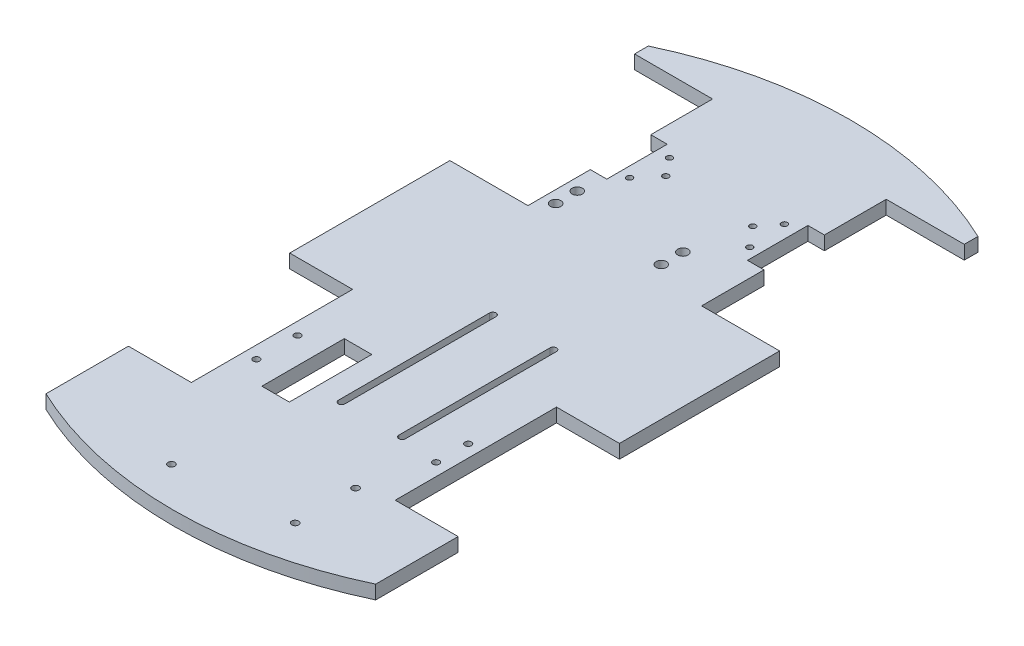
SolidWorks part; units mm, degrees
material "Oak"
ref_plane "Front Plane" through (0, 0, 0) normal (0, 0, 1) x (1, 0, 0)
ref_plane "Top Plane" through (0, 0, 0) normal (0, 1, 0) x (1, 0, 0)
ref_plane "Right Plane" through (0, 0, 0) normal (1, 0, 0) x (0, 0, -1)
sketch "Sketch1" plane through (0, 0, 0) normal (0, 1, 0) x (1, 0, 0)
  line L0 (50.292, 32.512) -> (76.2, 32.512) construction
  line L1 (0, 0) -> (0, -280.955) construction
  line L2 (0, 66.1738) -> (0, -229.362)
  line L3 (76.2, -229.362) -> (0, -229.362)
  line L7 (50.292, 32.512) -> (50.292, -32.512) construction
  line L8 (50.292, -32.512) -> (76.2, -32.512) construction
  line L9 (76.2, 32.512) -> (76.2, -32.512) construction
  line L10 (50.292, 32.512) -> (76.2, -32.512) construction
  line L11 (50.292, -32.512) -> (76.2, 32.512) construction
  line L18 (50.292, -119.888) -> (76.2, -119.888) construction
  line L19 (50.292, -119.888) -> (50.292, -184.912) construction
  line L20 (50.292, -184.912) -> (76.2, -184.912) construction
  line L21 (76.2, -119.888) -> (76.2, -184.912) construction
  line L22 (50.292, -119.888) -> (76.2, -184.912) construction
  line L23 (50.292, -184.912) -> (76.2, -119.888) construction
  line L25 (-76.2, 0) -> (76.2, 0) construction
  line L27 (-76.2, -152.4) -> (76.2, -152.4) construction
  line L28 (76.2, 0) -> (76.2, -152.4) construction
  line L33 (40.132, -42.672) -> (76.2, -42.672)
  line L34 (40.132, 42.672) -> (40.132, 14.097)
  line L35 (40.132, 42.672) -> (76.2, 42.672)
  line L36 (47.117, -191.262) -> (76.2, -191.262)
  line L37 (47.117, -116.713) -> (47.117, -191.262)
  line L38 (47.117, -116.713) -> (76.2, -116.713)
  line L43 (76.2, -42.672) -> (76.2, -116.713)
  line L45 (76.2, 42.672) -> (76.2, 49.022)
  line L47 (76.2, -191.262) -> (76.2, -229.362)
  line L55 (32.512, -13.843) -> (40.132, -13.843)
  line L56 (32.512, 14.097) -> (32.512, -13.843)
  line L57 (32.512, 14.097) -> (40.132, 14.097)
  line L58 (40.132, -13.843) -> (40.132, -42.672)
  arc A0 (0, 66.1738) -> (76.2, 49.022) centre (0, -111.6688) cw
  arc A1 (76.2, -229.362) -> (0, -252.984) centre (-13.2044, -75.675) cw
  point P9 (63.246, 0)
  point P19 (63.246, -152.4)
  dimension "D7" = 3.175
  dimension "D8" = 6.35
  dimension "D12" = 7.62
  dimension "D16" = 6.35
  dimension "D17" = 177.8426
  dimension "D18" = 177.8
  dimension "D1" = 152.4
  dimension "D2" = 152.4
  dimension "D3" = 126.492
  dimension "D4" = 25.908
  dimension "D6" = 3.175
  dimension "D9" = 10.16
  dimension "D10" = 10.16
  dimension "D5" = 65.024
  dimension "D11" = 10.16
  dimension "D13" = 27.94
  dimension "D14" = 28.575
  dimension "D15" = 38.1
  dimension "D19" = 23.622
extrude "Chassis" add sketch "Sketch1" along normal blind 6.35
mirror "Mirror1" about plane through (0, 6.35, 0) normal (1, 0, 0) of "Chassis"
sketch "Sketch4" plane through (0, 6.35, 0) normal (0, 1, 0) x (1, 0, 0)
  line L0 (76.2, -229.362) -> (-76.2, -229.362)
  arc A0 (76.2, -229.362) -> (-76.2, -229.362) centre (0, -68.7183) cw
  dimension "D1" = 177.8
extrude "Boss-Extrude1" add sketch "Sketch4" against normal blind 6.35 contours A0 L0
sketch "Sketch2" plane through (0, 0, 0) normal (0, 1, 0) x (1, 0, 0)
  line L0 (-47.117, -116.713) -> (-47.117, -191.262) construction
  line L1 (-47.117, -191.262) -> (-76.2, -191.262) construction
  line L2 (47.117, -116.713) -> (47.117, -191.262) construction
  line L3 (47.117, -191.262) -> (76.2, -191.262) construction
  line L4 (24.892, -94.488) -> (24.892, -164.338)
  line L5 (21.892, -94.488) -> (21.892, -164.338)
  line L6 (-3.048, -94.488) -> (-3.048, -164.338)
  line L7 (-6.048, -94.488) -> (-6.048, -164.338)
  line L8 (47.117, -116.713) -> (76.2, -116.713) construction
  line L10 (-16.637, -176.45) -> (-29.337, -176.45)
  line L11 (-16.637, -176.45) -> (-16.637, -138.35)
  line L12 (-16.637, -138.35) -> (-29.337, -138.35)
  line L13 (-29.337, -176.45) -> (-29.337, -138.35)
  circle A0 centre (-26.5557, 9.17) radius 1.3716 construction
  circle A2 centre (33.0969, -195.58) radius 1.5875
  circle A3 centre (-18.9731, -228.6) radius 1.5875
  circle A4 centre (-18.9731, -228.6) radius 1.5875
  circle A5 centre (33.0969, -223.52) radius 1.5875
  circle A6 centre (33.0969, -223.52) radius 1.5875
  circle A7 centre (-20.1056, 0.9994) radius 1.3716 construction
  circle A8 centre (-27.7865, -8.0406) radius 1.3716 construction
  circle A9 centre (26.5557, 9.17) radius 1.3716 construction
  circle A10 centre (20.1056, 0.9994) radius 1.3716 construction
  circle A11 centre (27.7865, -8.0406) radius 1.3716 construction
  circle A12 centre (14.2672, -25.46) radius 2.3813 construction
  circle A13 centre (14.2672, -35.4295) radius 2.3813 construction
  circle A14 centre (-34.5516, -25.46) radius 2.3813 construction
  circle A15 centre (-34.5516, -35.4295) radius 2.3813 construction
  circle A16 centre (41.402, -151.7963) radius 1.5
  arc A20 (24.892, -164.338) -> (21.892, -164.338) centre (23.392, -164.338) cw
  arc A21 (-3.048, -164.338) -> (-6.048, -164.338) centre (-4.548, -164.338) cw
  circle A24 centre (-26.5557, 9.17) radius 1.3716
  circle A25 centre (-20.1056, 0.9994) radius 1.3716
  circle A26 centre (-27.7865, -8.0406) radius 1.3716
  circle A27 centre (26.5557, 9.17) radius 1.3716
  circle A28 centre (20.1056, 0.9994) radius 1.3716
  circle A29 centre (27.7865, -8.0406) radius 1.3716
  circle A30 centre (14.2672, -25.46) radius 2.3812
  circle A31 centre (14.2672, -35.4295) radius 2.3813
  circle A32 centre (-34.5516, -25.46) radius 2.3813
  circle A33 centre (-34.5516, -35.4295) radius 2.3812
  arc A34 (24.892, -94.488) -> (21.892, -94.488) centre (23.392, -94.488) ccw
  arc A35 (-3.048, -94.488) -> (-6.048, -94.488) centre (-4.548, -94.488) ccw
  circle A38 centre (-41.402, -147.875) radius 1.5
  circle A39 centre (-41.402, -166.925) radius 1.5
  circle A41 centre (41.402, -166.6553) radius 1.5
  dimension "D4" = 3
  dimension "D5" = 3
  dimension "D10" = 3
  dimension "D14" = 3
  dimension "D15" = 5.715
  dimension "D22" = 22.225
  dimension "D26" = 3.175
  dimension "D6" = 19.05
  dimension "D7" = 5.715
  dimension "D8" = 5.715
  dimension "D9" = 24.337
  dimension "D11" = 14.859
  dimension "D12" = 5.715
  dimension "D13" = 24.6067
  dimension "D16" = 22.225
  dimension "D17" = 69.85
  dimension "D18" = 69.85
  dimension "D19" = 12.7
  dimension "D20" = 3
  dimension "D21" = 3
  dimension "1.1" = 27.94
  dimension "D23" = 30.48
  dimension "D24" = 38.1
  dimension "D25" = 9.525
  dimension "D2" = 0
  dimension "D3" = 0
extrude "Cut-Extrude1" cut sketch "Sketch2" along normal blind 17.78
